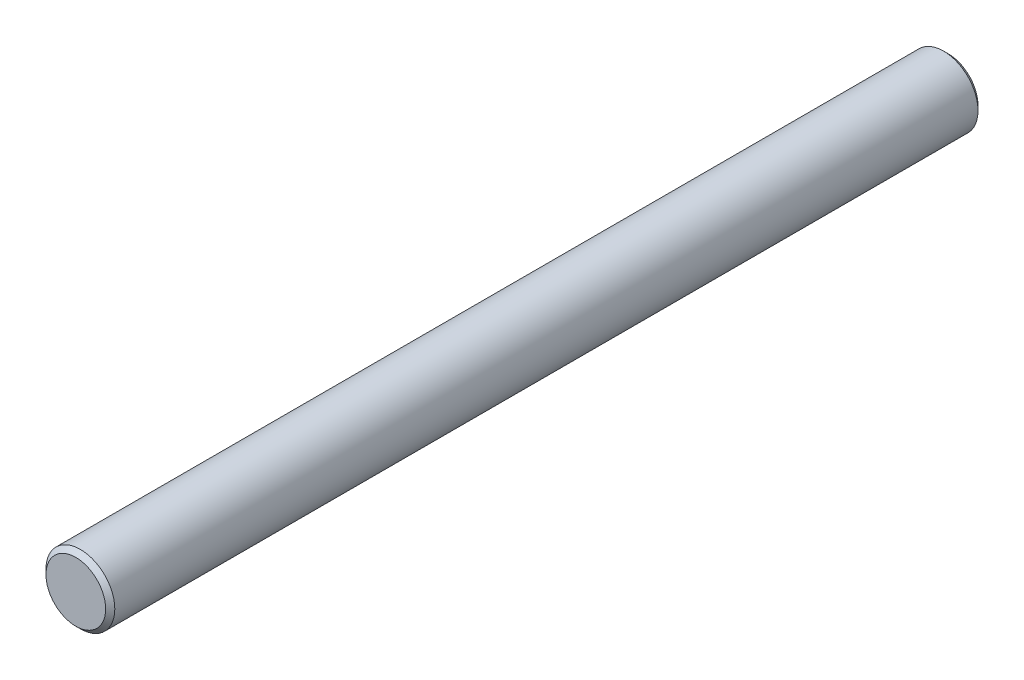
SolidWorks part; units mm, degrees
ref_plane "Front Plane" through (0, 0, 0) normal (0, 0, 1) x (1, 0, 0)
ref_plane "Top Plane" through (0, 0, 0) normal (0, 1, 0) x (1, 0, 0)
ref_plane "Right Plane" through (0, 0, 0) normal (1, 0, 0) x (0, 0, -1)
sketch "Sketch1" plane through (0, 0, 0) normal (0, 0, 1) x (1, 0, 0)
  circle A0 centre (0, 0) radius 0.75
  dimension "D1" = 1.5
extrude "Boss-Extrude1" add sketch "Sketch1" along normal blind 19
chamfer "Chamfer1" distance 0.1 angle 45 2 edges at (0.75, 0, 0) (0.75, 0, 19)
